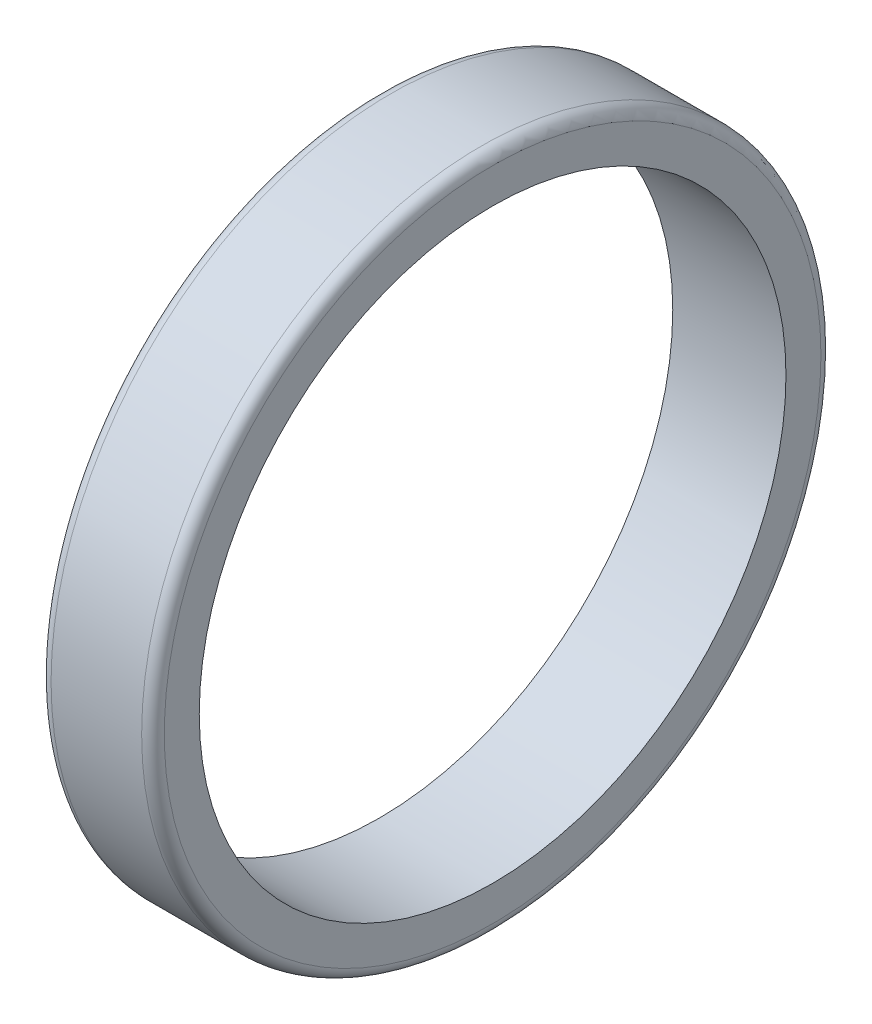
SolidWorks part; units mm, degrees
ref_plane "Front Plane" through (0, 0, 0) normal (0, 0, 1) x (1, 0, 0)
ref_plane "Top Plane" through (0, 0, 0) normal (0, 1, 0) x (1, 0, 0)
ref_plane "Right Plane" through (0, 0, 0) normal (1, 0, 0) x (0, 0, -1)
sketch "Sketch1" plane through (0, 0, 0) normal (1, 0, 0) x (0, 0, -1)
  circle A0 centre (0, 0) radius 65.8177
  circle A1 centre (0, 0) radius 76.2
  dimension "D1" = 131.6355
  dimension "D2" = 152.4
extrude "Boss-Extrude1" add sketch "Sketch1" along normal blind 25.4
fillet "Fillet1" radius 2.54 2 edges at (25.4, 0, -76.2) (0, 0, -76.2)
